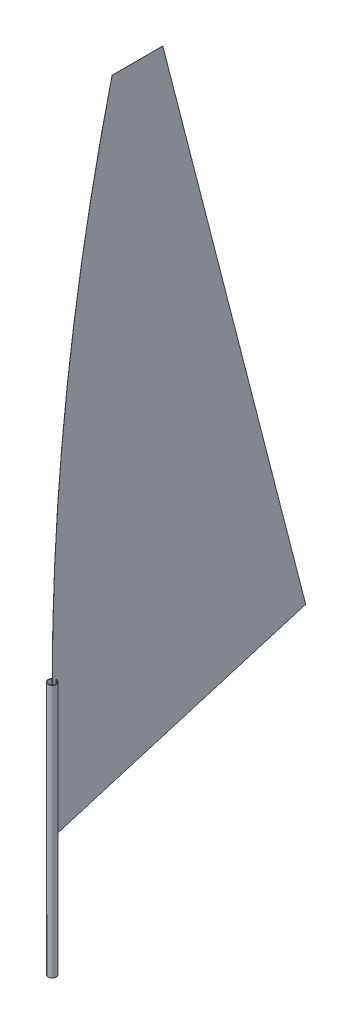
SolidWorks part; units mm, degrees
ref_plane "Front Plane" through (0, 0, 0) normal (0, 0, 1) x (1, 0, 0)
ref_plane "Top Plane" through (0, 0, 0) normal (0, 1, 0) x (1, 0, 0)
ref_plane "Right Plane" through (0, 0, 0) normal (1, 0, 0) x (0, 0, -1)
sketch "Sketch1" plane through (0, 0, 0) normal (1, 0, 0) x (0, 0, -1)
  line L0 (0, -1000) -> (0, 2000)
  dimension "D1" = 1000
  dimension "D2" = 2000
sketch "Sketch2" plane through (0, 0, 0) normal (0, 1, 0) x (1, 0, 0)
  circle A0 centre (0, 0) radius 50
  circle A1 centre (0, 0) radius 44
  dimension "D1" = 100
  dimension "D2" = 6
extrude "Boss-Extrude1" add sketch "Sketch2" along normal up to vertex (2000 mm away) and the other way up to vertex (1000 mm away) up to point (0, 2000, 0) other way up to point (0, -1000, 0)
sketch "Sketch4" plane through (0, 0, 0) normal (1, 0, 0) x (0, 0, -1)
  line L0 (0, 400) -> (3000, 1295.9979)
  line L1 (0, -1000) -> (0, 2000) construction
  line L2 (3000, 1295.9979) -> (1307.9305, 7866.5142)
  line L3 (1307.9305, 7866.5142) -> (707.9305, 7866.5142)
  line L4 (0, 400) -> (0, 2000)
  arc A0 (0, 2000) -> (707.9305, 7866.5142) centre (24661.4294, 2000) cw
  point P9 (0, 816.5393)
  point P10 (0, 0)
  point P11 (942.281, 13555.2516)
  point P12 (0, 0)
  point P13 (0, 2000)
  point P15 (0, 0)
  point P17 (4576.0349, 1148.9391)
  point P18 (1855.8685, 7374.8507)
  point P19 (3083.4876, 1295.9979)
  dimension "D1" = 7500
  dimension "D2" = 400
  dimension "D3" = 3000
  dimension "D4" = 600
extrude "Boss-Extrude2" add sketch "Sketch4" along normal mid plane 1 separate body
